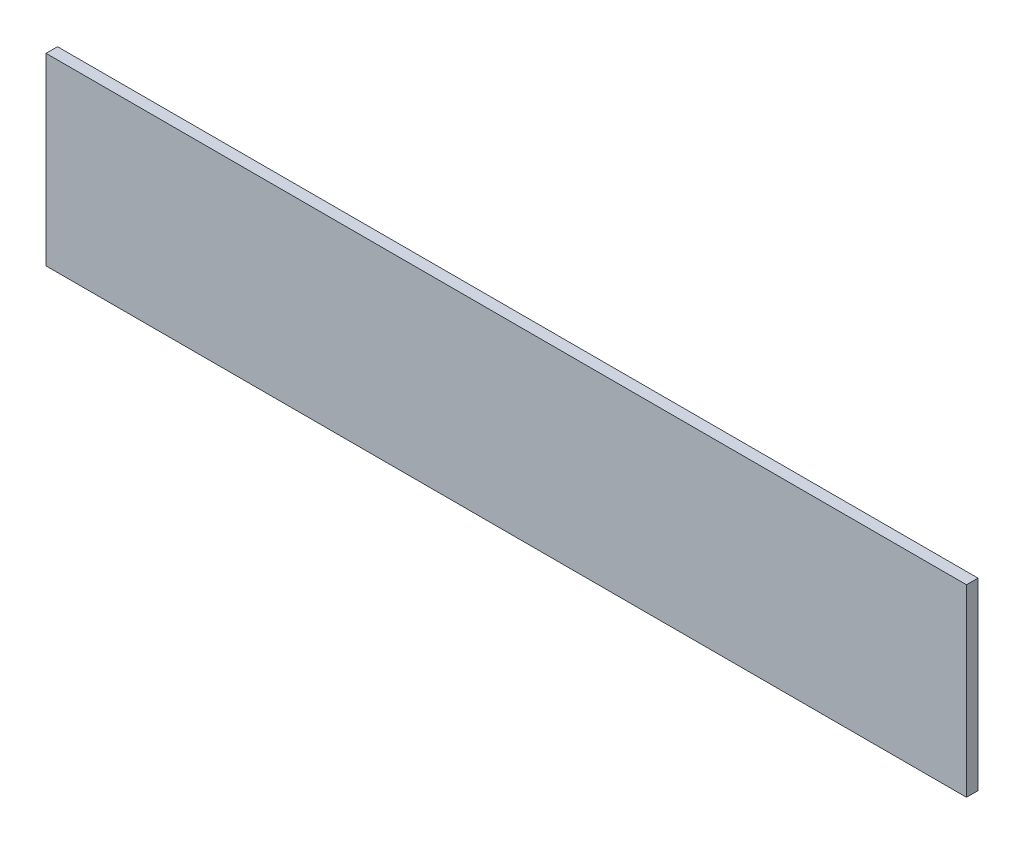
SolidWorks part; units mm, degrees
ref_plane "Front Plane" through (0, 0, 0) normal (0, 0, 1) x (1, 0, 0)
ref_plane "Top Plane" through (0, 0, 0) normal (0, 1, 0) x (1, 0, 0)
ref_plane "Right Plane" through (0, 0, 0) normal (1, 0, 0) x (0, 0, -1)
sketch "Sketch1" plane through (0, 0, 0) normal (0, 0, 1) x (1, 0, 0)
  line L1 (-127, -25.4) -> (127, -25.4)
  line L2 (-127, -25.4) -> (-127, 25.4)
  line L3 (-127, 25.4) -> (127, 25.4)
  line L4 (127, -25.4) -> (127, 25.4)
  line L5 (-127, -25.4) -> (127, 25.4) construction
  line L6 (-127, 25.4) -> (127, -25.4) construction
  point P0 (0, 0)
  dimension "D1" = 254
  dimension "D2" = 50.8
extrude "Boss-Extrude1" add sketch "Sketch1" along normal mid plane 3.175
